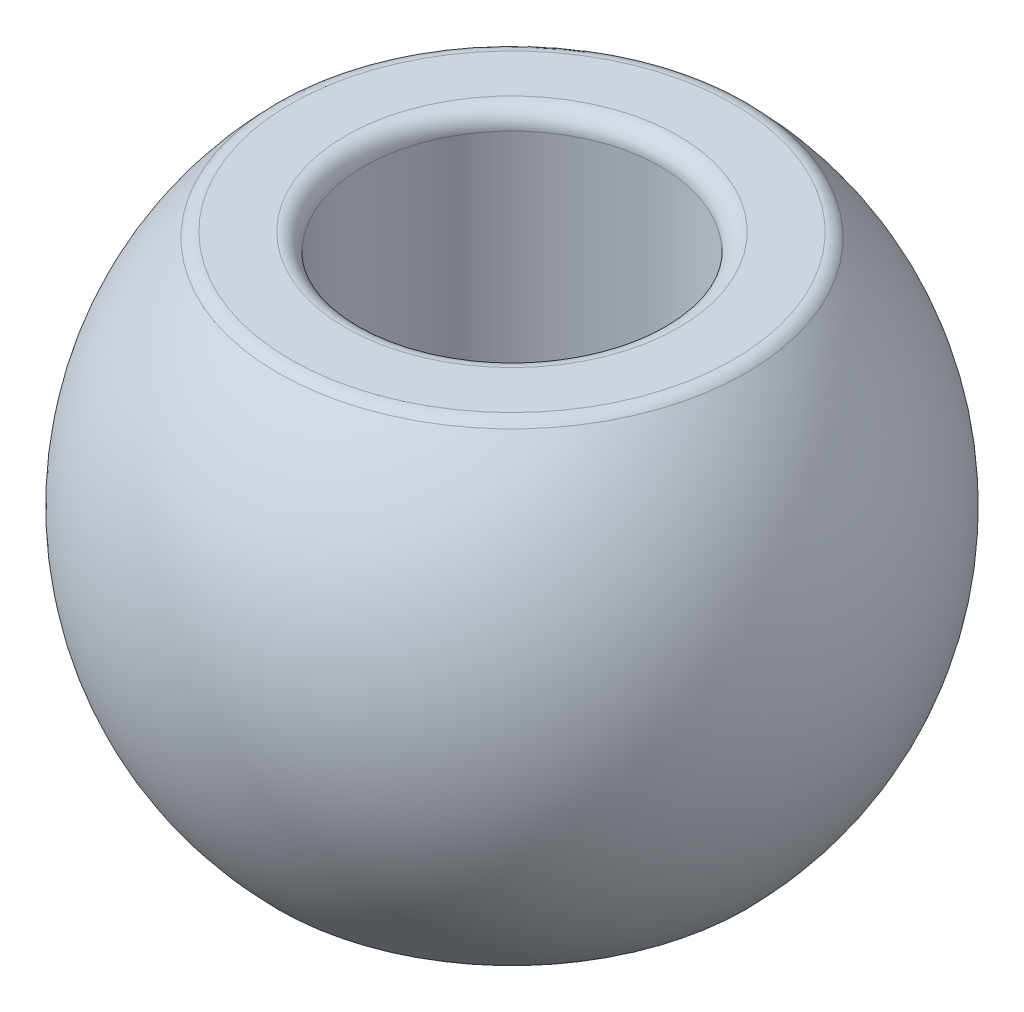
SolidWorks part; units mm, degrees
ref_plane "Front Plane" through (0, 0, 0) normal (0, 0, 1) x (1, 0, 0)
ref_plane "Top Plane" through (0, 0, 0) normal (0, 1, 0) x (1, 0, 0)
ref_plane "Right Plane" through (0, 0, 0) normal (1, 0, 0) x (0, 0, -1)
sketch "Sketch2" plane through (0, 0, 0) normal (0, 0, 1) x (1, 0, 0)
  line L0 (0, 0) -> (0, 3.3894) construction
  line L1 (2.5, -3.9981) -> (2.5, 3.9981)
  line L2 (2.5, 3.9981) -> (3.85, 3.9981)
  line L3 (2.5, -3.9981) -> (3.85, -3.9981)
  arc A0 (3.85, -3.9981) -> (3.85, 3.9981) centre (0, 0) ccw
  point P6 (2.5, 0)
  dimension "D1" = 7.9962
  dimension "D2" = 1.35
  dimension "D3" = 2.5
revolve "Revolve1" add sketch "Sketch2" angle 360 about L0
fillet "Fillet1" radius 0.3 4 edges at (0, 3.9981, -3.85) (0, 3.9981, -2.5) (0, -3.9981, -2.5) (0, -3.9981, -3.85)
